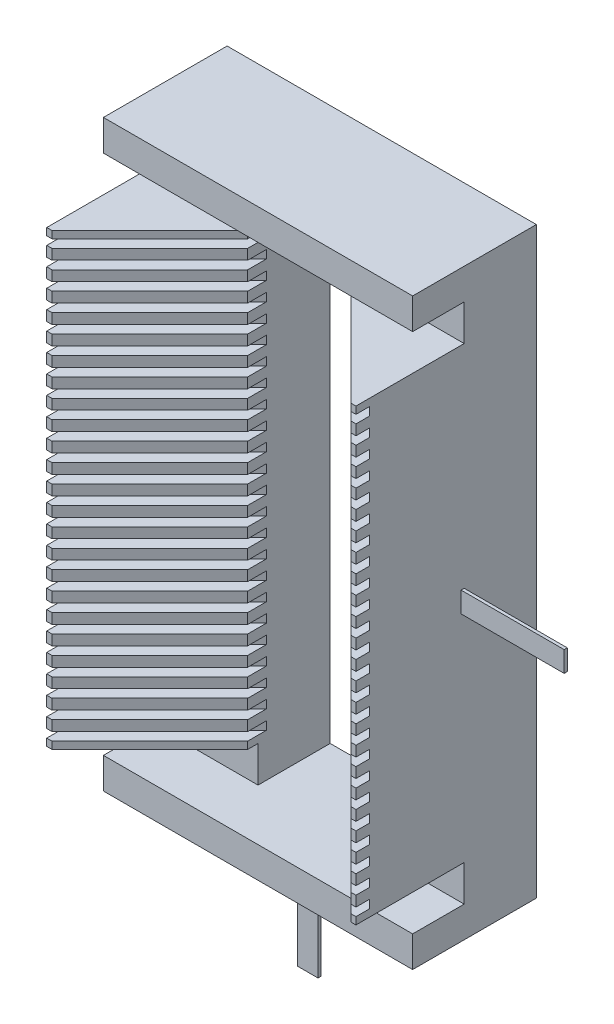
SolidWorks part; units mm, degrees
ref_plane "Front Plane" through (0, 0, 0) normal (0, 0, 1) x (1, 0, 0)
ref_plane "Top Plane" through (0, 0, 0) normal (0, 1, 0) x (1, 0, 0)
ref_plane "Right Plane" through (0, 0, 0) normal (1, 0, 0) x (0, 0, -1)
sketch "Sketch1" plane through (0, 0, 0) normal (0, 1, 0) x (1, 0, 0)
  line L0 (15, -17.5) -> (15, 0)
  line L1 (15, 0) -> (5, 0)
  line L2 (5, 0) -> (5, -8)
  line L3 (5, -8) -> (14.5, -17.5)
  line L4 (14.5, -17.5) -> (15, -17.5)
  line L5 (0, 0) -> (0, -17.5)
  line L6 (-14.5, -17.5) -> (-15, -17.5)
  line L7 (-5, -8) -> (-14.5, -17.5)
  line L8 (-5, 0) -> (-5, -8)
  line L9 (-15, 0) -> (-5, 0)
  line L10 (-15, -17.5) -> (-15, 0)
  line L11 (15, 0) -> (-15, 0)
  dimension "D1" = 10
  dimension "D2" = 0.5
  dimension "D3" = 17.5
  dimension "D4" = 8
  dimension "D5" = 10
extrude "Boss-Extrude1" add sketch "Sketch1" against normal mid plane 2.2 contours L3 L4 L0 L1 L2 | L10 L6 L7 L8 L9
sketch "Sketch2" plane through (0, 0, 0) normal (0, 1, 0) x (1, 0, 0)
  line L0 (-5, -8) -> (-5, -6.2)
  line L1 (-14.5, -17.5) -> (-15, -17.5)
  line L2 (-5, -6.2) -> (-15, -16.2)
  line L3 (15, -17.5) -> (15, -16.2)
  line L4 (-14.5, -17.5) -> (-5, -8)
  line L5 (14.5, -17.5) -> (5, -8)
  line L6 (5, -6.2) -> (15, -16.2)
  line L7 (0, 0) -> (0, -17.5)
  line L8 (14.5, -17.5) -> (15, -17.5)
  line L9 (5, -8) -> (5, -6.2)
  line L10 (-15, -17.5) -> (-15, -16.2)
  line L11 (-15, -17.5) -> (-15, 0) construction
  line L12 (-5, 0) -> (-5, -8) construction
  line L14 (15, 0) -> (-15, 0)
  dimension "D1" = 1.8
extrude "Cut-Extrude2" cut sketch "Sketch2" against normal mid plane 0.8
pattern_linear "LPattern1" count 24 spacing 1.8 along (0, 1, 0) of "Cut-Extrude2", "Boss-Extrude1"
sketch "Sketch4" plane through (0, 0, 0) normal (1, 0, 0) x (0, 0, -1)
  line L0 (0, -1.1) -> (0, -7.6)
  line L1 (0, -7.6) -> (-12, -7.6)
  line L2 (-12, -7.6) -> (-12, -4.6)
  line L3 (-12, -4.6) -> (-7, -4.6)
  line L4 (-7, -4.6) -> (-7, -1.1)
  line L5 (-7, -1.1) -> (0, -1.1)
  line L6 (-17.5, -1.1) -> (0, -1.1) construction
  line L7 (-12, 20.7) -> (0, 20.7)
  line L9 (-7, 42.5) -> (0, 42.5)
  line L10 (0, -1.1) -> (0, 42.5) construction
  line L11 (-7, 46) -> (-7, 42.5)
  line L12 (-12, 46) -> (-7, 46)
  line L13 (-12, 49) -> (-12, 46)
  line L14 (0, 49) -> (-12, 49)
  line L15 (0, 42.5) -> (0, 49)
  point P13 (0, 20.7)
  dimension "D1" = 7
  dimension "D2" = 12
  dimension "D3" = 3.5
  dimension "D4" = 3
extrude "Boss-Extrude3" add sketch "Sketch4" along normal mid plane 30 contours L1 L2 L3 L4 L5 L0 | L14 L13 L12 L11 L9 L15
sketch "Sketch11" plane through (0, 0, 12) normal (0, 0, 1) x (1, 0, 0)
  line L0 (-15, 41) -> (-15, 41.8) construction
  line L1 (-4.8, 41) -> (-15.5, 41)
  line L2 (-4.8, 41) -> (-4.8, 41.8)
  line L3 (-4.8, 41.8) -> (-15.5, 41.8)
  line L4 (-15.5, 41) -> (-15.5, 41.8)
  line L5 (15, 41) -> (15, 41.8) construction
  line L6 (4.8, 41.8) -> (15.5, 41.8)
  line L7 (4.8, 41.8) -> (4.8, 41)
  line L8 (4.8, 41) -> (15.5, 41)
  line L9 (15.5, 41.8) -> (15.5, 41)
  line L10 (-4.8, 39.2) -> (-15.5, 39.2)
  line L11 (-4.8, 39.2) -> (-4.8, 40)
  line L12 (-4.8, 40) -> (-15.5, 40)
  line L13 (-15.5, 39.2) -> (-15.5, 40)
  line L14 (4.8, 40) -> (15.5, 40)
  line L15 (4.8, 40) -> (4.8, 39.2)
  line L16 (4.8, 39.2) -> (15.5, 39.2)
  line L17 (15.5, 40) -> (15.5, 39.2)
  line L18 (-4.8, 37.4) -> (-15.5, 37.4)
  line L19 (-4.8, 37.4) -> (-4.8, 38.2)
  line L20 (-4.8, 38.2) -> (-15.5, 38.2)
  line L21 (-15.5, 37.4) -> (-15.5, 38.2)
  line L22 (4.8, 38.2) -> (15.5, 38.2)
  line L23 (4.8, 38.2) -> (4.8, 37.4)
  line L24 (4.8, 37.4) -> (15.5, 37.4)
  line L25 (15.5, 38.2) -> (15.5, 37.4)
  line L26 (-4.8, 35.6) -> (-15.5, 35.6)
  line L27 (-4.8, 35.6) -> (-4.8, 36.4)
  line L28 (-4.8, 36.4) -> (-15.5, 36.4)
  line L29 (-15.5, 35.6) -> (-15.5, 36.4)
  line L30 (4.8, 36.4) -> (15.5, 36.4)
  line L31 (4.8, 36.4) -> (4.8, 35.6)
  line L32 (4.8, 35.6) -> (15.5, 35.6)
  line L33 (15.5, 36.4) -> (15.5, 35.6)
  line L34 (-4.8, 33.8) -> (-15.5, 33.8)
  line L35 (-4.8, 33.8) -> (-4.8, 34.6)
  line L36 (-4.8, 34.6) -> (-15.5, 34.6)
  line L37 (-15.5, 33.8) -> (-15.5, 34.6)
  line L38 (4.8, 34.6) -> (15.5, 34.6)
  line L39 (4.8, 34.6) -> (4.8, 33.8)
  line L40 (4.8, 33.8) -> (15.5, 33.8)
  line L41 (15.5, 34.6) -> (15.5, 33.8)
  line L42 (-4.8, 32) -> (-15.5, 32)
  line L43 (-4.8, 32) -> (-4.8, 32.8)
  line L44 (-4.8, 32.8) -> (-15.5, 32.8)
  line L45 (-15.5, 32) -> (-15.5, 32.8)
  line L46 (4.8, 32.8) -> (15.5, 32.8)
  line L47 (4.8, 32.8) -> (4.8, 32)
  line L48 (4.8, 32) -> (15.5, 32)
  line L49 (15.5, 32.8) -> (15.5, 32)
  line L50 (-4.8, 30.2) -> (-15.5, 30.2)
  line L51 (-4.8, 30.2) -> (-4.8, 31)
  line L52 (-4.8, 31) -> (-15.5, 31)
  line L53 (-15.5, 30.2) -> (-15.5, 31)
  line L54 (4.8, 31) -> (15.5, 31)
  line L55 (4.8, 31) -> (4.8, 30.2)
  line L56 (4.8, 30.2) -> (15.5, 30.2)
  line L57 (15.5, 31) -> (15.5, 30.2)
  line L58 (-4.8, 28.4) -> (-15.5, 28.4)
  line L59 (-4.8, 28.4) -> (-4.8, 29.2)
  line L60 (-4.8, 29.2) -> (-15.5, 29.2)
  line L61 (-15.5, 28.4) -> (-15.5, 29.2)
  line L62 (4.8, 29.2) -> (15.5, 29.2)
  line L63 (4.8, 29.2) -> (4.8, 28.4)
  line L64 (4.8, 28.4) -> (15.5, 28.4)
  line L65 (15.5, 29.2) -> (15.5, 28.4)
  line L66 (-4.8, 26.6) -> (-15.5, 26.6)
  line L67 (-4.8, 26.6) -> (-4.8, 27.4)
  line L68 (-4.8, 27.4) -> (-15.5, 27.4)
  line L69 (-15.5, 26.6) -> (-15.5, 27.4)
  line L70 (4.8, 27.4) -> (15.5, 27.4)
  line L71 (4.8, 27.4) -> (4.8, 26.6)
  line L72 (4.8, 26.6) -> (15.5, 26.6)
  line L73 (15.5, 27.4) -> (15.5, 26.6)
  line L74 (-4.8, 24.8) -> (-15.5, 24.8)
  line L75 (-4.8, 24.8) -> (-4.8, 25.6)
  line L76 (-4.8, 25.6) -> (-15.5, 25.6)
  line L77 (-15.5, 24.8) -> (-15.5, 25.6)
  line L78 (4.8, 25.6) -> (15.5, 25.6)
  line L79 (4.8, 25.6) -> (4.8, 24.8)
  line L80 (4.8, 24.8) -> (15.5, 24.8)
  line L81 (15.5, 25.6) -> (15.5, 24.8)
  line L82 (-4.8, 23) -> (-15.5, 23)
  line L83 (-4.8, 23) -> (-4.8, 23.8)
  line L84 (-4.8, 23.8) -> (-15.5, 23.8)
  line L85 (-15.5, 23) -> (-15.5, 23.8)
  line L86 (4.8, 23.8) -> (15.5, 23.8)
  line L87 (4.8, 23.8) -> (4.8, 23)
  line L88 (4.8, 23) -> (15.5, 23)
  line L89 (15.5, 23.8) -> (15.5, 23)
  line L90 (-4.8, 21.2) -> (-15.5, 21.2)
  line L91 (-4.8, 21.2) -> (-4.8, 22)
  line L92 (-4.8, 22) -> (-15.5, 22)
  line L93 (-15.5, 21.2) -> (-15.5, 22)
  line L94 (4.8, 22) -> (15.5, 22)
  line L95 (4.8, 22) -> (4.8, 21.2)
  line L96 (4.8, 21.2) -> (15.5, 21.2)
  line L97 (15.5, 22) -> (15.5, 21.2)
  line L98 (-4.8, 19.4) -> (-15.5, 19.4)
  line L99 (-4.8, 19.4) -> (-4.8, 20.2)
  line L100 (-4.8, 20.2) -> (-15.5, 20.2)
  line L101 (-15.5, 19.4) -> (-15.5, 20.2)
  line L102 (4.8, 20.2) -> (15.5, 20.2)
  line L103 (4.8, 20.2) -> (4.8, 19.4)
  line L104 (4.8, 19.4) -> (15.5, 19.4)
  line L105 (15.5, 20.2) -> (15.5, 19.4)
  line L106 (-4.8, 17.6) -> (-15.5, 17.6)
  line L107 (-4.8, 17.6) -> (-4.8, 18.4)
  line L108 (-4.8, 18.4) -> (-15.5, 18.4)
  line L109 (-15.5, 17.6) -> (-15.5, 18.4)
  line L110 (4.8, 18.4) -> (15.5, 18.4)
  line L111 (4.8, 18.4) -> (4.8, 17.6)
  line L112 (4.8, 17.6) -> (15.5, 17.6)
  line L113 (15.5, 18.4) -> (15.5, 17.6)
  line L114 (-4.8, 15.8) -> (-15.5, 15.8)
  line L115 (-4.8, 15.8) -> (-4.8, 16.6)
  line L116 (-4.8, 16.6) -> (-15.5, 16.6)
  line L117 (-15.5, 15.8) -> (-15.5, 16.6)
  line L118 (4.8, 16.6) -> (15.5, 16.6)
  line L119 (4.8, 16.6) -> (4.8, 15.8)
  line L120 (4.8, 15.8) -> (15.5, 15.8)
  line L121 (15.5, 16.6) -> (15.5, 15.8)
  line L122 (-4.8, 14) -> (-15.5, 14)
  line L123 (-4.8, 14) -> (-4.8, 14.8)
  line L124 (-4.8, 14.8) -> (-15.5, 14.8)
  line L125 (-15.5, 14) -> (-15.5, 14.8)
  line L126 (4.8, 14.8) -> (15.5, 14.8)
  line L127 (4.8, 14.8) -> (4.8, 14)
  line L128 (4.8, 14) -> (15.5, 14)
  line L129 (15.5, 14.8) -> (15.5, 14)
  line L130 (-4.8, 12.2) -> (-15.5, 12.2)
  line L131 (-4.8, 12.2) -> (-4.8, 13)
  line L132 (-4.8, 13) -> (-15.5, 13)
  line L133 (-15.5, 12.2) -> (-15.5, 13)
  line L134 (4.8, 13) -> (15.5, 13)
  line L135 (4.8, 13) -> (4.8, 12.2)
  line L136 (4.8, 12.2) -> (15.5, 12.2)
  line L137 (15.5, 13) -> (15.5, 12.2)
  line L138 (-4.8, 10.4) -> (-15.5, 10.4)
  line L139 (-4.8, 10.4) -> (-4.8, 11.2)
  line L140 (-4.8, 11.2) -> (-15.5, 11.2)
  line L141 (-15.5, 10.4) -> (-15.5, 11.2)
  line L142 (4.8, 11.2) -> (15.5, 11.2)
  line L143 (4.8, 11.2) -> (4.8, 10.4)
  line L144 (4.8, 10.4) -> (15.5, 10.4)
  line L145 (15.5, 11.2) -> (15.5, 10.4)
  line L146 (-4.8, 8.6) -> (-15.5, 8.6)
  line L147 (-4.8, 8.6) -> (-4.8, 9.4)
  line L148 (-4.8, 9.4) -> (-15.5, 9.4)
  line L149 (-15.5, 8.6) -> (-15.5, 9.4)
  line L150 (4.8, 9.4) -> (15.5, 9.4)
  line L151 (4.8, 9.4) -> (4.8, 8.6)
  line L152 (4.8, 8.6) -> (15.5, 8.6)
  line L153 (15.5, 9.4) -> (15.5, 8.6)
  line L154 (-4.8, 6.8) -> (-15.5, 6.8)
  line L155 (-4.8, 6.8) -> (-4.8, 7.6)
  line L156 (-4.8, 7.6) -> (-15.5, 7.6)
  line L157 (-15.5, 6.8) -> (-15.5, 7.6)
  line L158 (4.8, 7.6) -> (15.5, 7.6)
  line L159 (4.8, 7.6) -> (4.8, 6.8)
  line L160 (4.8, 6.8) -> (15.5, 6.8)
  line L161 (15.5, 7.6) -> (15.5, 6.8)
  line L162 (-4.8, 5) -> (-15.5, 5)
  line L163 (-4.8, 5) -> (-4.8, 5.8)
  line L164 (-4.8, 5.8) -> (-15.5, 5.8)
  line L165 (-15.5, 5) -> (-15.5, 5.8)
  line L166 (4.8, 5.8) -> (15.5, 5.8)
  line L167 (4.8, 5.8) -> (4.8, 5)
  line L168 (4.8, 5) -> (15.5, 5)
  line L169 (15.5, 5.8) -> (15.5, 5)
  line L170 (-4.8, 3.2) -> (-15.5, 3.2)
  line L171 (-4.8, 3.2) -> (-4.8, 4)
  line L172 (-4.8, 4) -> (-15.5, 4)
  line L173 (-15.5, 3.2) -> (-15.5, 4)
  line L174 (4.8, 4) -> (15.5, 4)
  line L175 (4.8, 4) -> (4.8, 3.2)
  line L176 (4.8, 3.2) -> (15.5, 3.2)
  line L177 (15.5, 4) -> (15.5, 3.2)
  line L178 (-4.8, 1.4) -> (-15.5, 1.4)
  line L179 (-4.8, 1.4) -> (-4.8, 2.2)
  line L180 (-4.8, 2.2) -> (-15.5, 2.2)
  line L181 (-15.5, 1.4) -> (-15.5, 2.2)
  line L182 (4.8, 2.2) -> (15.5, 2.2)
  line L183 (4.8, 2.2) -> (4.8, 1.4)
  line L184 (4.8, 1.4) -> (15.5, 1.4)
  line L185 (15.5, 2.2) -> (15.5, 1.4)
  line L186 (-4.8, -0.4) -> (-15.5, -0.4)
  line L187 (-4.8, -0.4) -> (-4.8, 0.4)
  line L188 (-4.8, 0.4) -> (-15.5, 0.4)
  line L189 (-15.5, -0.4) -> (-15.5, 0.4)
  line L190 (4.8, 0.4) -> (15.5, 0.4)
  line L191 (4.8, 0.4) -> (4.8, -0.4)
  line L192 (4.8, -0.4) -> (15.5, -0.4)
  line L193 (15.5, 0.4) -> (15.5, -0.4)
  line L194 (-5, 41) -> (-5, 41.8) construction
  line L195 (5, 41) -> (5, 41.8) construction
  dimension "D1" = 0.5
  dimension "D2" = 0.5
  dimension "D4" = 0.2
  dimension "D5" = 0.2
  dimension "D3" = 24
sketch "Sketch6" plane through (0, 0, 0) normal (0, 0, -1) x (-1, 0, 0)
  line L0 (-15, 49) -> (-15, -7.6) construction
  line L1 (15, -17.6) -> (-25, -17.6)
  line L2 (15, -17.6) -> (15, 49)
  line L3 (15, 49) -> (-25, 49)
  line L4 (-25, -17.6) -> (-25, 49)
  line L5 (15, -17.6) -> (-25, 49) construction
  line L6 (15, 49) -> (-25, -17.6) construction
  line L7 (-15, 49) -> (15, 49) construction
  line L8 (-15, -7.6) -> (15, -7.6) construction
  line L9 (15, -7.6) -> (15, 49) construction
  point P0 (-5, 15.7)
  dimension "D1" = 10
  dimension "D2" = 0
  dimension "D3" = 10
  dimension "D4" = 0
sketch "Sketch9" plane through (0, 0, 7) normal (0, 0, -1) x (-1, 0, 0)
  line L0 (-15, 49) -> (-15, -7.6) construction
  line L1 (-15, 21.9349) -> (-25, 21.9349)
  line L2 (-15, 21.9349) -> (-15, 19.9349)
  line L3 (-15, 19.9349) -> (-25, 19.9349)
  line L4 (-25, 21.9349) -> (-25, 19.9349)
  line L5 (-15, -7.6) -> (15, -7.6) construction
  line L6 (-1.1136, -7.6) -> (0.8864, -7.6)
  line L7 (-1.1136, -7.6) -> (-1.1136, -17.6)
  line L8 (-1.1136, -17.6) -> (0.8864, -17.6)
  line L9 (0.8864, -7.6) -> (0.8864, -17.6)
  dimension "D1" = 10
  dimension "D2" = 10
  dimension "D3" = 2
  dimension "D4" = 2
extrude "Boss-Extrude4" add sketch "Sketch9" against normal blind 0.3
sketch "Sketch12" plane through (0, 0, 7) normal (0, 0, 1) x (1, 0, 0)
  line L0 (15, -4.6) -> (-15, -4.6) construction
  line L1 (5, -1.1) -> (-5, -1.1)
  line L2 (5, -1.1) -> (5, -4.6)
  line L3 (5, -4.6) -> (-5, -4.6)
  line L4 (-5, -1.1) -> (-5, -4.6)
  line L5 (15, 46) -> (-15, 46) construction
  line L6 (5, 42.5) -> (-5, 42.5)
  line L7 (5, 42.5) -> (5, 46)
  line L8 (5, 46) -> (-5, 46)
  line L9 (-5, 42.5) -> (-5, 46)
extrude "Cut-Extrude3" cut sketch "Sketch12" against normal through all both and the other way through all
equation "\"D1@Boss-Extrude3\"=22"
